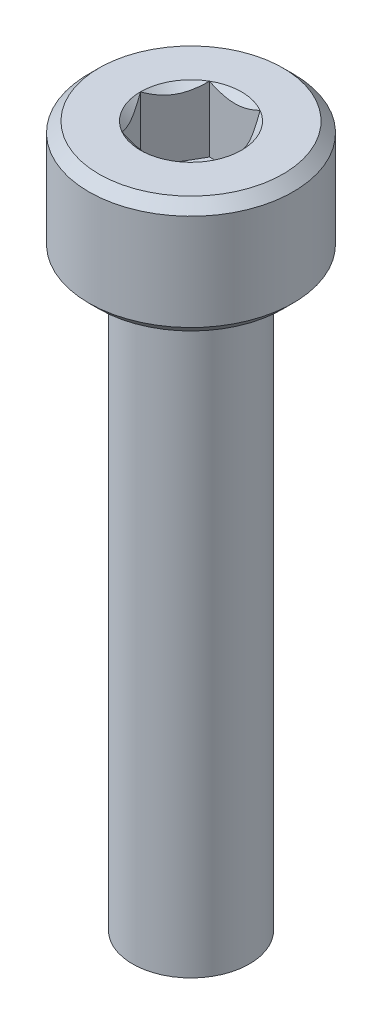
SolidWorks part; units mm, degrees
ref_plane "Front" through (0, 0, 0) normal (0, 0, 1) x (1, 0, 0)
ref_plane "Top" through (0, 0, 0) normal (0, 1, 0) x (1, 0, 0)
ref_plane "Right" through (0, 0, 0) normal (1, 0, 0) x (0, 0, -1)
sketch "Sketch1" plane through (0, 0, 0) normal (0, 1, 0) x (1, 0, 0)
  circle A0 centre (0, 0) radius 3.5
  dimension "D1" = 7
extrude "Boss-Extrude1" add sketch "Sketch1" along normal blind 4
sketch "Sketch2" plane through (0, 4, 0) normal (0, 1, 0) x (1, 0, 0)
  line L1 (0.866, 1.5) -> (-0.866, 1.5)
  line L2 (-0.866, 1.5) -> (-1.7321, 0)
  line L3 (-1.7321, 0) -> (-0.866, -1.5)
  line L4 (-0.866, -1.5) -> (0.866, -1.5)
  line L5 (0.866, -1.5) -> (1.7321, 0)
  line L6 (1.7321, 0) -> (0.866, 1.5)
  circle A0 centre (0, 0) radius 1.5 construction
  point P10 (0, 1.5)
  dimension "D1" = 3
extrude "Cut-Extrude1" cut sketch "Sketch2" against normal blind 2.25
sketch "Sketch3" plane through (0, 4, 0) normal (0, 1, 0) x (1, 0, 0)
  circle A0 centre (0, 0) radius 1.7321
extrude "Cut-Extrude2" cut sketch "Sketch3" against normal through all draft 45
chamfer "Chamfer1" distance 0.35 angle 45 2 edges at (0, 0, 3.5) (0, 4, 3.5)
sketch "草图1" plane through (0, 0, 0) normal (0, -1, 0) x (-1, 0, 0)
  circle A0 centre (0, 0) radius 2
  dimension "D1" = 4
extrude "凸台-拉伸1" add sketch "草图1" along normal blind 20
